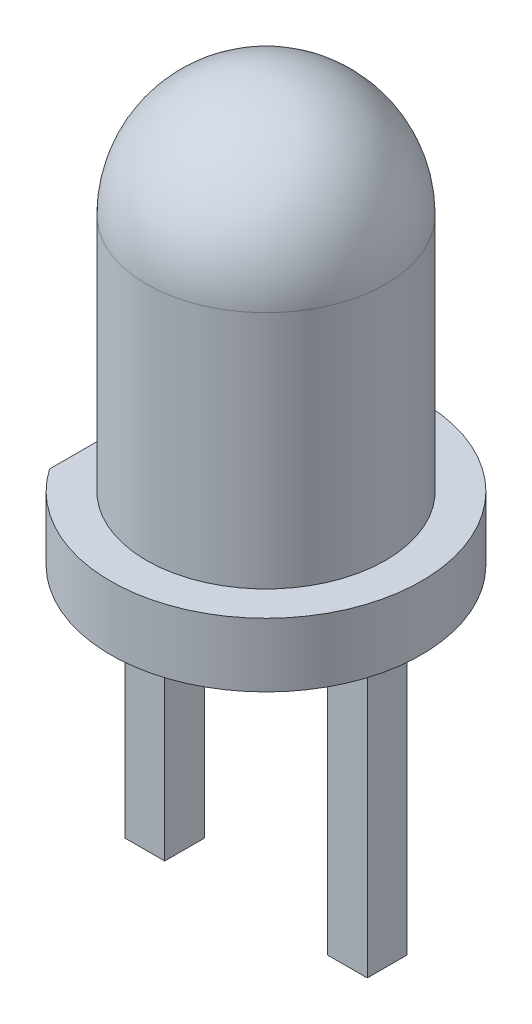
SolidWorks part; units mm, degrees
ref_plane "Plan de face" through (0, 0, 0) normal (0, 0, 1) x (1, 0, 0)
ref_plane "Plan de dessus" through (0, 0, 0) normal (0, 1, 0) x (1, 0, 0)
ref_plane "Plan de droite" through (0, 0, 0) normal (1, 0, 0) x (0, 0, -1)
sketch "Esquisse1" plane through (0, 0, 0) normal (0, 0, 1) x (1, 0, 0)
  line L0 (0, 0) -> (-1.95, 0)
  line L1 (-1.95, 0) -> (-1.95, 0.8)
  line L2 (-1.95, 0.8) -> (-1.5, 0.8)
  line L3 (-1.5, 0.8) -> (-1.5, 3.8)
  line L4 (0, 5.3) -> (0, 0)
  arc A0 (-1.5, 3.8) -> (0, 5.3) centre (0, 3.8) cw
  dimension "D1" = 1.5
  dimension "D2" = 5.3
  dimension "D3" = 1.95
  dimension "D4" = 0.8
revolve "Révolution1" add sketch "Esquisse1" angle 360 about L4
sketch "Esquisse2" plane through (0, 0, 0) normal (0, -1, 0) x (1, 0, 0)
  line L0 (-1.27, 0) -> (0, 0) construction
  line L1 (-1.52, -0.25) -> (-1.02, -0.25)
  line L2 (-1.52, -0.25) -> (-1.52, 0.25)
  line L3 (-1.52, 0.25) -> (-1.02, 0.25)
  line L4 (-1.02, -0.25) -> (-1.02, 0.25)
  line L5 (-1.52, -0.25) -> (-1.02, 0.25) construction
  line L6 (-1.52, 0.25) -> (-1.02, -0.25) construction
  line L7 (1.02, -0.25) -> (1.52, -0.25)
  line L8 (1.02, -0.25) -> (1.02, 0.25)
  line L9 (1.02, 0.25) -> (1.52, 0.25)
  line L10 (1.52, -0.25) -> (1.52, 0.25)
  line L11 (1.02, -0.25) -> (1.52, 0.25) construction
  line L12 (1.02, 0.25) -> (1.52, -0.25) construction
  line L13 (0, 0) -> (1.27, 0) construction
  point P0 (-1.27, 0)
  point P5 (1.27, 0)
  dimension "D1" = 2.54
  dimension "D2" = 0.5
extrude "Boss.-Extru.1" add sketch "Esquisse2" along normal blind 3.6
sketch "Esquisse3" plane through (0, 0, 0) normal (0, -1, 0) x (1, 0, 0)
  line L0 (-2.1, 0) -> (0.0527, 0) construction
  line L1 (-2.6, -2) -> (-1.6, -2)
  line L2 (-2.6, -2) -> (-2.6, 2)
  line L3 (-2.6, 2) -> (-1.6, 2)
  line L4 (-1.6, -2) -> (-1.6, 2)
  line L5 (-2.6, -2) -> (-1.6, 2) construction
  line L6 (-2.6, 2) -> (-1.6, -2) construction
  point P0 (-2.1, 0)
  dimension "D1" = 1.6
  dimension "D2" = 1
  dimension "D3" = 4
extrude "Enlèv. mat.-Extru.1" cut sketch "Esquisse3" against normal through all
